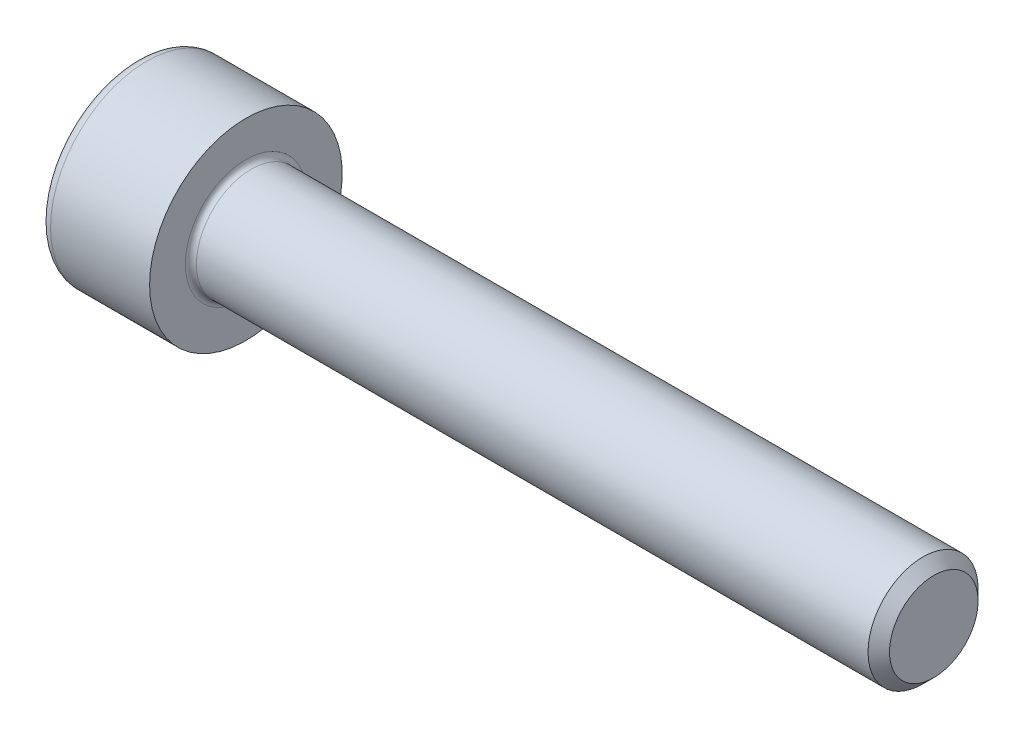
SolidWorks part; units mm, degrees
revolve "Base-Revolve" add sketch "BodySke"
sketch "BodySke" plane through (0, 0, 0) normal (0, 0, 1) x (1, 0, 0)
  line L0 (0, 0) -> (0, 3.5)
  line L1 (0, 3.5) -> (4, 3.5)
  line L2 (4, 3.5) -> (4, 2)
  line L3 (4, 2) -> (28.61, 2)
  line L4 (29, 1.61) -> (29, 0)
  line L5 (29, 0) -> (0, 0)
  line L6 (-31.75, 0) -> (127, 0) construction
  line L8 (29, 1.61) -> (28.61, 2)
  line L10 (29, -1.61) -> (28.61, -2) construction
  line L11 (4.7, 9.525) -> (4.7, 3.175) construction
  line L12 (9, 9.525) -> (9, 3.175) construction
  line L13 (13.0069, 9.525) -> (13.0069, 3.175) construction
  dimension "Head_ht" = 4
  dimension "Length" = 25
  dimension "Body_ch_ang" = 45
  dimension "Diameter" = 4
  dimension "Minor_dia" = 3.22
  dimension "Advance" = 0.7
  dimension "Thread_nom" = 20
  dimension "Thread_length" = 15.9931
  dimension "Head_dia" = 7
cosmetic thread "ThreadCosmetic" [suppressed]
fillet "Fillet1" radius 0.2 1 edges at (4, 0, 2)
fillet "Fillet2" radius 0.4 1 edges at (0, 0, 3.5)
ref_plane "Plane1" through (0, 0, 0) normal (0, 0, 1) x (1, 0, 0)
ref_plane "Plane2" through (0, 0, 0) normal (0, 1, 0) x (1, 0, 0)
ref_plane "Plane3" through (0, 0, 0) normal (1, 0, 0) x (0, 0, -1)
sketch "Sketch2" plane through (0, 0, 0) normal (0, 0, 1) x (1, 0, 0)
  line L0 (0, 1.51) -> (2, 1.51)
  line L1 (2, 1.51) -> (2.8718, 0)
  line L2 (-31.75, 0) -> (127, 0) construction
  line L3 (2.8718, 0) -> (0, 0)
  line L4 (0, 0) -> (0, 1.51)
  line L6 (0, 0) -> (47.625, 0) construction
  dimension "D1" = 1.51
  dimension "D2" = 60
  dimension "Depth" = 2
revolve "Hex-PreBroach" cut sketch "Sketch2" angle 360 about L6
sketch "Sketch3" plane through (0, 0, 0) normal (-1, 0, 0) x (0, 0.5, 0.866)
  line L0 (0.8718, 1.51) -> (-0.8718, 1.51)
  line L1 (-0.8718, 1.51) -> (-1.7436, 0)
  line L2 (0.8718, 1.51) -> (1.7436, 0)
  line L3 (0.8718, -1.51) -> (1.7436, 0)
  line L4 (0.8718, -1.51) -> (-0.8718, -1.51)
  line L5 (-0.8718, -1.51) -> (-1.7436, 0)
  dimension "D1" = 1.51
  dimension "D2" = 1.51
  dimension "Hex_size" = 3.02
extrude "Hex" cut sketch "Sketch3" against normal blind 2
sketch "ThdSchSke" plane through (0, 0, 0) normal (0, 0, 1) x (1, 0, 0)
  line L0 (6.1, -1.61) -> (5.8269, -2)
  line L1 (6.1, -1.61) -> (6.3731, -2)
  line L2 (6.3731, -2) -> (6.3731, -2.5)
  line L3 (-3.175, 0) -> (5.1513, 0) construction
  line L4 (0, 3.1) -> (0, -3.1) construction
  line L5 (6.3731, -2.5) -> (5.8269, -2.5)
  line L6 (5.8269, -2.5) -> (5.8269, -2)
  dimension "Thread_minor" = 3.22
  dimension "Diameter" = 4
  dimension "Start" = 6.1
revolve "ThreadSchematic" [suppressed] cut sketch "ThdSchSke" angle 360 about L3
pattern_linear "ThdSchPat" [suppressed]
equation "\"D2@Sketch3\" = \"Hex_size@Sketch3\" / 2"
equation "\"D1@Sketch3\" = \"Hex_size@Sketch3\" / 2"
equation "\"D1@Sketch2\" = \"Hex_size@Sketch3\" / 2"
equation "\"Thread_minor@ThreadCosmetic\"  =  \"Minor_dia@BodySke\""
equation "\"Depth@Sketch2\" =  \"Key_eng@Hex\""
equation "\"Thread_length@ThreadCosmetic\" = ((sgn( (\"Length@BodySke\" - \"Advance@BodySke\" * 3.0) - \"Thread_nom@BodySke\" )-1)*( (\"Length@BodySke\" - \"Advance@BodySke\" * 3.0) - \"Thread_nom@BodySke\" ))/-2+ \"Thread_nom@BodySke\""
equation "\"Thread_minor@ThdSchSke\" = \"Minor_dia@BodySke\""
equation "\"Diameter@ThdSchSke\" = \"Diameter@BodySke\""
equation "\"Overcut@ThdSchSke\" = \"Diameter@BodySke\" * 1.25"
equation "\"Start@ThdSchSke\" = \"Head_ht@BodySke\" + \"Length@BodySke\" - \"Thread_length@ThreadCosmetic\"  '---Non-countersunk---"
equation "\"Num_threads@ThdSchPat\" = int( \"Thread_length@ThreadCosmetic\" / \"Advance@BodySke\" + 0.999 )  + 1"
equation "\"Advance@ThdSchPat\" = \"Thread_length@ThreadCosmetic\" /  (\"Num_threads@ThdSchPat\" - 1) 'relax it"
equation "\"Num_threads@ThdSchPat\" = \"Num_threads@ThdSchPat\" - sgn( \"Num_threads@ThdSchPat\" - 1) '---chamfered tips only---"
